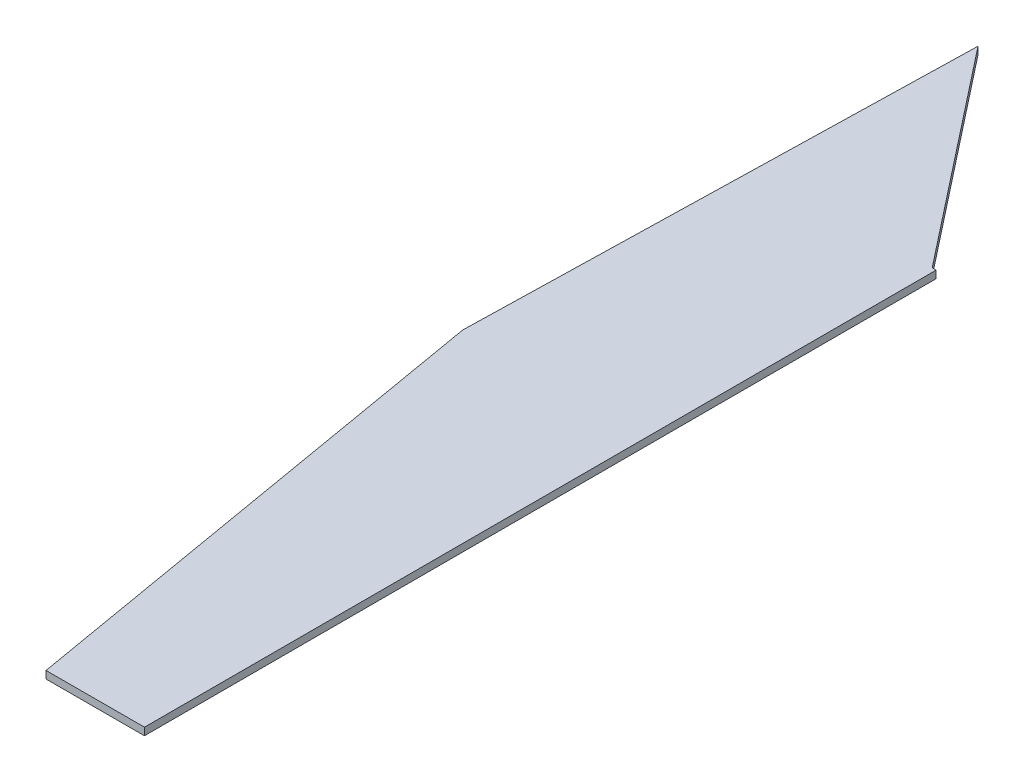
SolidWorks part; units mm, degrees
ref_plane "Plan de face" through (0, 0, 0) normal (0, 0, 1) x (1, 0, 0)
ref_plane "Plan de dessus" through (0, 0, 0) normal (0, 1, 0) x (1, 0, 0)
ref_plane "Plan de droite" through (0, 0, 0) normal (1, 0, 0) x (0, 0, -1)
sketch "Esquisse1" plane through (0, 0, 0) normal (0, 1, 0) x (1, 0, 0)
  line L0 (-23.1783, 134.88) -> (0, 0)
  line L1 (0, 0) -> (26.3621, 0.0322)
  line L2 (26.3621, 0.0322) -> (26.3621, 212.2161)
  line L3 (26.3621, 212.2161) -> (25.2862, 212.2415)
  line L4 (25.2862, 212.2415) -> (-19.9944, 269.7922)
  line L5 (-19.9944, 269.7922) -> (-23.1783, 134.88)
  point P6 (0, 0)
extrude "Boss.-Extru.1" add sketch "Esquisse1" along normal blind 2
